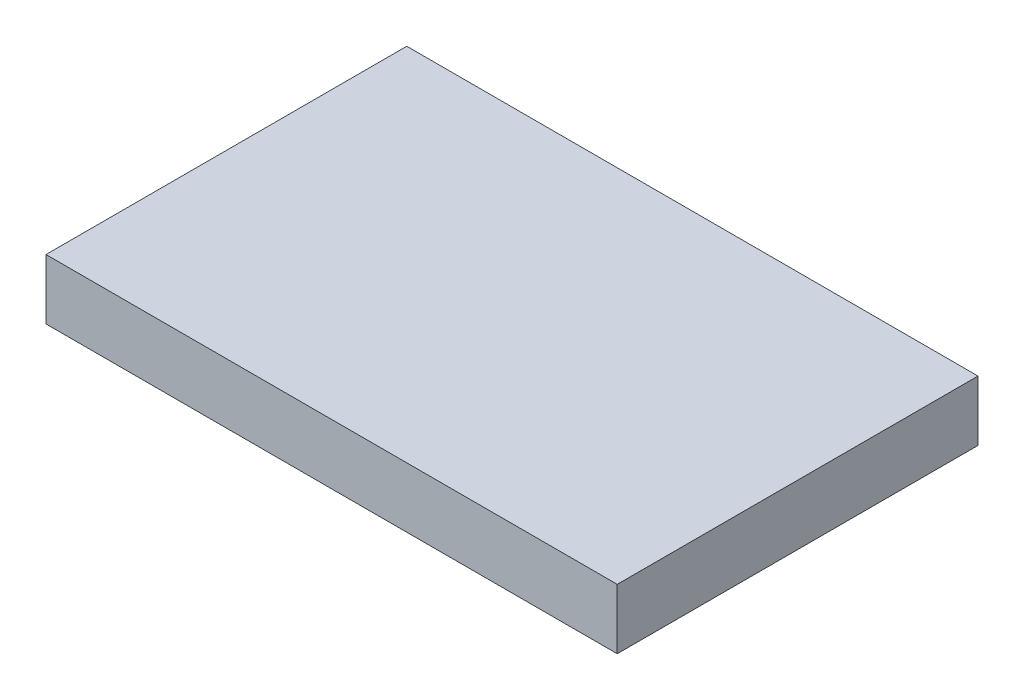
SolidWorks part; units mm, degrees
ref_plane "Front" through (0, 0, 0) normal (0, 0, 1) x (1, 0, 0)
ref_plane "Top" through (0, 0, 0) normal (0, 1, 0) x (1, 0, 0)
ref_plane "Right" through (0, 0, 0) normal (1, 0, 0) x (0, 0, -1)
sketch "Sketch1" plane through (0, 0, 0) normal (0, 1, 0) x (1, 0, 0)
  line L1 (0, 0) -> (38, 0)
  line L2 (0, 0) -> (0, -24)
  line L3 (0, -24) -> (38, -24)
  line L4 (38, 0) -> (38, -24)
  dimension "D1" = 38
  dimension "D2" = 24
extrude "Boss-Extrude1" add sketch "Sketch1" along normal blind 4
